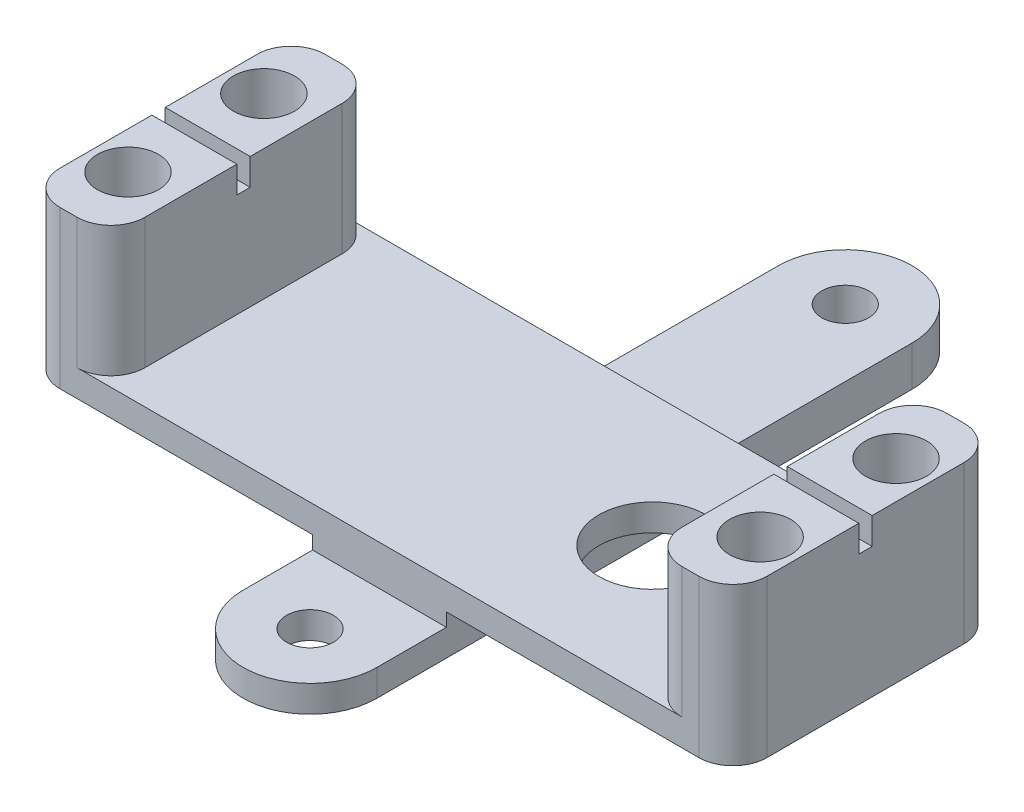
SolidWorks part; units mm, degrees
ref_plane "Plan de face" through (0, 0, 0) normal (0, 0, 1) x (1, 0, 0)
ref_plane "Plan de dessus" through (0, 0, 0) normal (0, 1, 0) x (1, 0, 0)
ref_plane "Plan de droite" through (0, 0, 0) normal (1, 0, 0) x (0, 0, -1)
sketch "Esquisse2" plane through (0, 0, 0) normal (0, 1, 0) x (1, 0, 0)
  line L2 (-4.9991, 19.9068) -> (-4.9991, -20.0932)
  line L4 (5, 20) -> (5, -20)
  arc A0 (5, 20) -> (-4.9991, 19.9068) centre (0, 20) ccw
  arc A1 (-4.9991, -20.0932) -> (5, -20) centre (0, -20) ccw
  point P5 (5, 0)
  dimension "D2" = 5
  dimension "D1" = 40
extrude "Boss.-Extru.1" add sketch "Esquisse2" along normal blind 3
sketch "Esquisse3" plane through (0, 3, 0) normal (0, 1, 0) x (1, 0, 0)
  circle A0 centre (0, 20) radius 1.75
  circle A1 centre (0, -20) radius 1.75
  dimension "D1" = 3.5
  dimension "D2" = 3.5
extrude "Enlèv. mat.-Extru.1" cut sketch "Esquisse3" against normal up to next
sketch "Esquisse4" plane through (0, 3, 0) normal (0, 1, 0) x (1, 0, 0)
  line L1 (-26.415, 5) -> (26.415, 5)
  line L2 (-26.415, 5) -> (-26.415, -14.81)
  line L3 (-26.415, -14.81) -> (26.415, -14.81)
  line L4 (26.415, 5) -> (26.415, -14.81)
  point P4 (0, 5)
  dimension "D1" = 52.83
  dimension "D2" = 19.81
  dimension "D3" = 5
extrude "Boss.-Extru.2" add sketch "Esquisse4" along normal blind 2
sketch "Esquisse6" plane through (0, 5, 0) normal (0, 1, 0) x (1, 0, 0)
  line L0 (26.415, 5) -> (-26.415, 5) construction
  line L1 (-20.065, 5) -> (-26.415, 5)
  line L2 (-20.065, 5) -> (-20.065, -14.81)
  line L3 (-20.065, -14.81) -> (-26.415, -14.81)
  line L4 (-26.415, 5) -> (-26.415, -14.81)
  dimension "D1" = 6.35
extrude "Boss.-Extru.3" add sketch "Esquisse6" along normal blind 9.74
sketch "Esquisse5" plane through (0, 5, 0) normal (0, 1, 0) x (1, 0, 0)
  line L0 (-26.415, 5) -> (-26.415, -14.81) construction
  line L2 (26.415, 5) -> (-20.065, 5) construction
  line L3 (-20.065, -14.81) -> (26.415, -14.81) construction
  circle A0 centre (-23.621, 0.174) radius 2.286
  circle A1 centre (-23.621, -9.984) radius 2.286
  dimension "D1" = 2.794
  dimension "D2" = 4.572
  dimension "D3" = 4.572
  dimension "D4" = 4.826
  dimension "D5" = 4.826
extrude "Enlèv. mat.-Extru.2" cut sketch "Esquisse5" against normal through all both and the other way through all
mirror "Symétrie1" about plane through (0, 0, 0) normal (1, 0, 0) of "Enlèv. mat.-Extru.2", "Boss.-Extru.3"
sketch "Esquisse7" plane through (0, 5, 0) normal (0, 1, 0) x (1, 0, 0)
  line L0 (26.415, 5) -> (26.415, -14.81) construction
  circle A0 centre (10.415, -4.8242) radius 4
  dimension "D1" = 8
  dimension "D2" = 16
extrude "Enlèv. mat.-Extru.3" cut sketch "Esquisse7" against normal through all
sketch "Esquisse8" plane through (26.415, 0, 0) normal (1, 0, 0) x (0, 0, -1)
  line L0 (5, 14.74) -> (-14.81, 14.74) construction
  line L1 (-5.405, 14.74) -> (-4.405, 14.74)
  line L2 (-5.405, 14.74) -> (-5.405, 12.74)
  line L3 (-5.405, 12.74) -> (-4.405, 12.74)
  line L4 (-4.405, 14.74) -> (-4.405, 12.74)
  point P6 (-4.905, 14.74)
  point P7 (-4.905, 14.74)
  dimension "D1" = 1
  dimension "D2" = 2
extrude "Enlèv. mat.-Extru.4" cut sketch "Esquisse8" against normal through all
sketch "Esquisse9" plane through (5, 0, 0) normal (1, 0, 0) x (0, 0, -1)
  line L1 (-14.81, 3) -> (-25, 3)
  line L2 (-14.81, 3) -> (-14.81, 2)
  line L3 (-14.81, 2) -> (-25, 2)
  line L4 (-25, 3) -> (-25, 2)
  dimension "D1" = 1
extrude "Enlèv. mat.-Extru.5" cut sketch "Esquisse9" against normal through all
fillet "Congé1" radius 2.54 4 edges at (-26.415, 8.87, -5) (-26.415, 8.87, 14.81) (26.415, 8.87, -5) (26.415, 8.87, 14.81)
fillet "Congé2" radius 2.54 4 edges at (20.065, 9.87, -5) (20.065, 9.87, 14.81) (-20.065, 9.87, -5) (-20.065, 9.87, 14.81)
